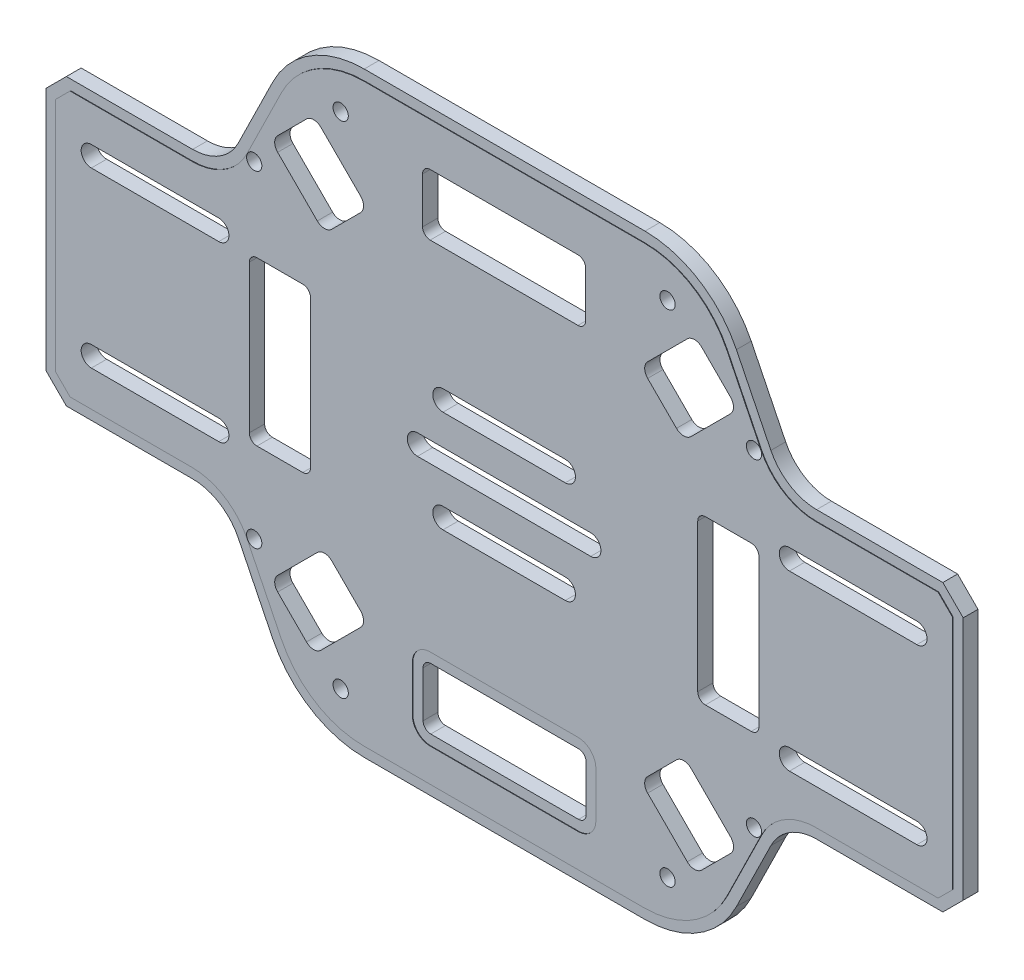
SolidWorks part; units mm, degrees
ref_plane "Alzado" through (0, 0, 0) normal (0, 0, 1) x (1, 0, 0)
ref_plane "Planta" through (0, 0, 0) normal (0, 1, 0) x (1, 0, 0)
ref_plane "Vista lateral" through (0, 0, 0) normal (1, 0, 0) x (0, 0, -1)
sketch "Croquis1" plane through (0, 0, 0) normal (0, 0, 1) x (1, 0, 0)
  line L0 (0, -28) -> (0, 28)
  line L1 (90, 0) -> (90, 79.6309) construction
  line L2 (117.5482, 58.5) -> (62.4518, 58.5)
  line L3 (180, 28) -> (151.2259, 28)
  line L4 (142.2524, 33.5868) -> (135.4952, 47.3264)
  line L5 (0, -28) -> (28.7741, -28)
  line L6 (180, 28) -> (180, -28)
  line L7 (0, 0) -> (180, 0) construction
  line L8 (0, 28) -> (28.7741, 28)
  line L9 (37.7476, 33.5868) -> (44.5048, 47.3264)
  line L10 (37.7476, -33.5868) -> (44.5048, -47.3264)
  line L11 (117.5482, -58.5) -> (62.4518, -58.5)
  line L12 (142.2524, -33.5868) -> (135.4952, -47.3264)
  line L13 (180, -28) -> (151.2259, -28)
  line L14 (78, -8) -> (102, -8)
  line L15 (107, -2) -> (73, -2)
  line L16 (78, 12) -> (102, 12)
  line L17 (107, 2) -> (73, 2)
  line L18 (78, -12) -> (102, -12)
  line L19 (78, 8) -> (102, 8)
  line L20 (106, -46.5) -> (106, -37.5)
  line L21 (75.5, 48) -> (104.5, 48)
  line L22 (74, 46.5) -> (74, 37.5)
  line L23 (75.5, 36) -> (104.5, 36)
  line L24 (40, 14.5) -> (40, -14.5)
  line L25 (106, 46.5) -> (106, 37.5)
  line L26 (74, 48) -> (106, 36) construction
  line L27 (74, 36) -> (106, 48) construction
  line L28 (74, -46.5) -> (74, -37.5)
  line L29 (75.5, -48) -> (104.5, -48)
  line L30 (75.5, -36) -> (104.5, -36)
  line L31 (146, -19) -> (171, -19)
  line L32 (129.5, 16) -> (138.5, 16)
  line L33 (128, 14.5) -> (128, -14.5)
  line L34 (129.5, -16) -> (138.5, -16)
  line L35 (140, 14.5) -> (140, -14.5)
  line L36 (128, 16) -> (140, -16) construction
  line L37 (128, -16) -> (140, 16) construction
  line L38 (50.5, -16) -> (41.5, -16)
  line L39 (52, 14.5) -> (52, -14.5)
  line L40 (50.5, 16) -> (41.5, 16)
  line L41 (146, 19) -> (171, 19)
  line L42 (146, -15) -> (171, -15)
  line L43 (146, 15) -> (171, 15)
  line L44 (34, -15) -> (9, -15)
  line L45 (34, -19) -> (9, -19)
  line L46 (34, 19) -> (9, 19)
  line L47 (34, 15) -> (9, 15)
  arc A0 (44.5048, 47.3264) -> (62.4518, 58.5) centre (62.4518, 38.5) cw
  arc A1 (28.7741, 28) -> (37.7476, 33.5868) centre (28.7741, 38) ccw
  arc A2 (151.2259, 28) -> (142.2524, 33.5868) centre (151.2259, 38) cw
  arc A3 (135.4952, 47.3264) -> (117.5482, 58.5) centre (117.5482, 38.5) ccw
  arc A4 (28.7741, -28) -> (37.7476, -33.5868) centre (28.7741, -38) cw
  arc A5 (44.5048, -47.3264) -> (62.4518, -58.5) centre (62.4518, -38.5) ccw
  arc A6 (135.4952, -47.3264) -> (117.5482, -58.5) centre (117.5482, -38.5) cw
  arc A7 (151.2259, -28) -> (142.2524, -33.5868) centre (151.2259, -38) ccw
  arc A8 (73, 2) -> (73, -2) centre (73, 0) ccw
  arc A9 (107, -2) -> (107, 2) centre (107, 0) ccw
  arc A10 (78, 12) -> (78, 8) centre (78, 10) ccw
  arc A11 (102, 8) -> (102, 12) centre (102, 10) ccw
  arc A12 (78, -12) -> (78, -8) centre (78, -10) cw
  arc A13 (102, -8) -> (102, -12) centre (102, -10) cw
  arc A14 (104.5, 36) -> (106, 37.5) centre (104.5, 37.5) ccw
  arc A15 (104.5, 48) -> (106, 46.5) centre (104.5, 46.5) cw
  arc A16 (75.5, 48) -> (74, 46.5) centre (75.5, 46.5) ccw
  arc A17 (74, 37.5) -> (75.5, 36) centre (75.5, 37.5) ccw
  arc A18 (104.5, -36) -> (106, -37.5) centre (104.5, -37.5) cw
  arc A19 (104.5, -48) -> (106, -46.5) centre (104.5, -46.5) ccw
  arc A20 (75.5, -48) -> (74, -46.5) centre (75.5, -46.5) cw
  arc A21 (74, -37.5) -> (75.5, -36) centre (75.5, -37.5) cw
  arc A22 (138.5, -16) -> (140, -14.5) centre (138.5, -14.5) ccw
  arc A23 (128, -14.5) -> (129.5, -16) centre (129.5, -14.5) ccw
  arc A24 (138.5, 16) -> (140, 14.5) centre (138.5, 14.5) cw
  arc A25 (129.5, 16) -> (128, 14.5) centre (129.5, 14.5) ccw
  arc A26 (50.5, 16) -> (52, 14.5) centre (50.5, 14.5) cw
  arc A27 (41.5, 16) -> (40, 14.5) centre (41.5, 14.5) ccw
  arc A28 (41.5, -16) -> (40, -14.5) centre (41.5, -14.5) cw
  arc A29 (52, -14.5) -> (50.5, -16) centre (50.5, -14.5) cw
  arc A30 (146, 19) -> (146, 15) centre (146, 17) ccw
  arc A31 (171, 15) -> (171, 19) centre (171, 17) ccw
  arc A32 (171, -15) -> (171, -19) centre (171, -17) cw
  arc A33 (146, -19) -> (146, -15) centre (146, -17) cw
  arc A34 (34, -19) -> (34, -15) centre (34, -17) ccw
  arc A35 (9, -15) -> (9, -19) centre (9, -17) ccw
  arc A36 (9, 15) -> (9, 19) centre (9, 17) cw
  arc A37 (34, 19) -> (34, 15) centre (34, 17) cw
  point P15 (50, 58.5)
  point P18 (35, 28)
  point P22 (90, 58.5)
  point P41 (90, 10)
  point P55 (90, 42)
  point P84 (134, 0)
  point P113 (158.5, 17)
  dimension "D7" = 20
  dimension "D8" = 10
  dimension "D16" = 1.5
  dimension "D20" = 1.5
  dimension "D1" = 180
  dimension "D2" = 28
  dimension "D3" = 40
  dimension "D4" = 4
  dimension "D5" = 35
  dimension "D6" = 58.5
  dimension "D9" = 34
  dimension "D10" = 24
  dimension "D11" = 4
  dimension "D12" = 10
  dimension "D13" = 12
  dimension "D14" = 32
  dimension "D15" = 42
  dimension "D17" = 32
  dimension "D18" = 12
  dimension "D19" = 44
  dimension "D21" = 25
  dimension "D22" = 4
  dimension "D23" = 17
  dimension "D24" = 24.5
extrude "Saliente-Extruir1" add sketch "Croquis1" along normal mid plane 3
chamfer "Chaflán1" distance 4 angle 45 4 edges at (0, 28, 0) (0, -28, 0) (180, 28, 0) (180, -28, 0)
sketch "Croquis2" plane through (0, 0, 1.5) normal (0, 0, 1) x (1, 0, 0)
  line L0 (117.5482, 58.5) -> (62.4518, 58.5) construction
  line L1 (142.2524, 33.5868) -> (135.4952, 47.3264) construction
  line L2 (176, 28) -> (151.2259, 28) construction
  line L3 (180, 24) -> (176, 28) construction
  line L4 (180, -24) -> (180, 24) construction
  line L5 (176, -28) -> (180, -24) construction
  line L6 (151.2259, -28) -> (176, -28) construction
  line L7 (135.4952, -47.3264) -> (142.2524, -33.5868) construction
  line L8 (62.4518, -58.5) -> (117.5482, -58.5) construction
  line L9 (37.7476, -33.5868) -> (44.5048, -47.3264) construction
  line L10 (4, -28) -> (28.7741, -28) construction
  line L11 (0, -24) -> (4, -28) construction
  line L12 (0, 24) -> (0, -24) construction
  line L13 (4, 28) -> (0, 24) construction
  line L14 (28.7741, 28) -> (4, 28) construction
  line L15 (44.5048, 47.3264) -> (37.7476, 33.5868) construction
  line L16 (117.5482, 58.5) -> (62.4518, 58.5)
  line L17 (142.2524, 33.5868) -> (135.4952, 47.3264)
  line L18 (176, 28) -> (151.2259, 28)
  line L19 (180, 24) -> (176, 28)
  line L20 (180, -24) -> (180, 24)
  line L21 (176, -28) -> (180, -24)
  line L22 (151.2259, -28) -> (176, -28)
  line L23 (135.4952, -47.3264) -> (142.2524, -33.5868)
  line L24 (62.4518, -58.5) -> (117.5482, -58.5)
  line L25 (37.7476, -33.5868) -> (44.5048, -47.3264)
  line L26 (4, -28) -> (28.7741, -28)
  line L27 (0, -24) -> (4, -28)
  line L28 (0, 24) -> (0, -24)
  line L29 (4, 28) -> (0, 24)
  line L30 (28.7741, 28) -> (4, 28)
  line L31 (44.5048, 47.3264) -> (37.7476, 33.5868)
  line L32 (140.4577, 32.7042) -> (133.7005, 46.4438)
  line L33 (117.5482, 56.5) -> (62.4518, 56.5)
  line L34 (46.2995, 46.4438) -> (39.5423, 32.7042)
  line L35 (28.7741, 26) -> (4.8284, 26)
  line L36 (4.8284, 26) -> (2, 23.1716)
  line L37 (2, 23.1716) -> (2, -23.1716)
  line L38 (2, -23.1716) -> (4.8284, -26)
  line L39 (4.8284, -26) -> (28.7741, -26)
  line L40 (39.5423, -32.7042) -> (46.2995, -46.4438)
  line L41 (62.4518, -56.5) -> (117.5482, -56.5)
  line L42 (133.7005, -46.4438) -> (140.4577, -32.7042)
  line L43 (151.2259, -26) -> (175.1716, -26)
  line L44 (175.1716, -26) -> (178, -23.1716)
  line L45 (178, -23.1716) -> (178, 23.1716)
  line L46 (178, 23.1716) -> (175.1716, 26)
  line L47 (175.1716, 26) -> (151.2259, 26)
  arc A0 (62.4518, 58.5) -> (44.5048, 47.3264) centre (62.4518, 38.5) ccw construction
  arc A1 (135.4952, 47.3264) -> (117.5482, 58.5) centre (117.5482, 38.5) ccw construction
  arc A2 (142.2524, 33.5868) -> (151.2259, 28) centre (151.2259, 38) ccw construction
  arc A3 (151.2259, -28) -> (142.2524, -33.5868) centre (151.2259, -38) ccw construction
  arc A4 (117.5482, -58.5) -> (135.4952, -47.3264) centre (117.5482, -38.5) ccw construction
  arc A5 (44.5048, -47.3264) -> (62.4518, -58.5) centre (62.4518, -38.5) ccw construction
  arc A6 (37.7476, -33.5868) -> (28.7741, -28) centre (28.7741, -38) ccw construction
  arc A7 (28.7741, 28) -> (37.7476, 33.5868) centre (28.7741, 38) ccw construction
  arc A8 (62.4518, 58.5) -> (44.5048, 47.3264) centre (62.4518, 38.5) ccw
  arc A9 (135.4952, 47.3264) -> (117.5482, 58.5) centre (117.5482, 38.5) ccw
  arc A10 (142.2524, 33.5868) -> (151.2259, 28) centre (151.2259, 38) ccw
  arc A11 (151.2259, -28) -> (142.2524, -33.5868) centre (151.2259, -38) ccw
  arc A12 (117.5482, -58.5) -> (135.4952, -47.3264) centre (117.5482, -38.5) ccw
  arc A13 (44.5048, -47.3264) -> (62.4518, -58.5) centre (62.4518, -38.5) ccw
  arc A14 (37.7476, -33.5868) -> (28.7741, -28) centre (28.7741, -38) ccw
  arc A15 (28.7741, 28) -> (37.7476, 33.5868) centre (28.7741, 38) ccw
  arc A16 (133.7005, 46.4438) -> (117.5482, 56.5) centre (117.5482, 38.5) ccw
  arc A17 (62.4518, 56.5) -> (46.2995, 46.4438) centre (62.4518, 38.5) ccw
  arc A18 (28.7741, 26) -> (39.5423, 32.7042) centre (28.7741, 38) ccw
  arc A19 (39.5423, -32.7042) -> (28.7741, -26) centre (28.7741, -38) ccw
  arc A20 (46.2995, -46.4438) -> (62.4518, -56.5) centre (62.4518, -38.5) ccw
  arc A21 (117.5482, -56.5) -> (133.7005, -46.4438) centre (117.5482, -38.5) ccw
  arc A22 (151.2259, -26) -> (140.4577, -32.7042) centre (151.2259, -38) ccw
  arc A23 (140.4577, 32.7042) -> (151.2259, 26) centre (151.2259, 38) ccw
  dimension "D1" = 2
extrude "Cortar-Extruir1" cut sketch "Croquis2" against normal blind 0.1
sketch "Croquis3" plane through (0, 0, 1.5) normal (0, 0, 1) x (1, 0, 0)
  line L0 (74, -37.5) -> (74, -46.5) construction
  line L1 (75.5, -48) -> (104.5, -48) construction
  line L2 (106, -46.5) -> (106, -37.5) construction
  line L3 (104.5, -36) -> (75.5, -36) construction
  line L4 (74, -37.5) -> (74, -46.5)
  line L5 (75.5, -48) -> (104.5, -48)
  line L6 (106, -46.5) -> (106, -37.5)
  line L7 (104.5, -36) -> (75.5, -36)
  line L8 (72, -37.5) -> (72, -46.5)
  line L9 (75.5, -50) -> (104.5, -50)
  line L10 (108, -46.5) -> (108, -37.5)
  line L11 (104.5, -34) -> (75.5, -34)
  arc A0 (104.5, -48) -> (106, -46.5) centre (104.5, -46.5) ccw construction
  arc A1 (106, -37.5) -> (104.5, -36) centre (104.5, -37.5) ccw construction
  arc A2 (75.5, -36) -> (74, -37.5) centre (75.5, -37.5) ccw construction
  arc A3 (74, -46.5) -> (75.5, -48) centre (75.5, -46.5) ccw construction
  arc A4 (104.5, -48) -> (106, -46.5) centre (104.5, -46.5) ccw
  arc A5 (106, -37.5) -> (104.5, -36) centre (104.5, -37.5) ccw
  arc A6 (75.5, -36) -> (74, -37.5) centre (75.5, -37.5) ccw
  arc A7 (74, -46.5) -> (75.5, -48) centre (75.5, -46.5) ccw
  arc A8 (72, -46.5) -> (75.5, -50) centre (75.5, -46.5) ccw
  arc A9 (104.5, -50) -> (108, -46.5) centre (104.5, -46.5) ccw
  arc A10 (108, -37.5) -> (104.5, -34) centre (104.5, -37.5) ccw
  arc A11 (75.5, -34) -> (72, -37.5) centre (75.5, -37.5) ccw
  dimension "D1" = 2
extrude "Cortar-Extruir2" cut sketch "Croquis3" against normal blind 0.1
sketch "Croquis4" plane through (0, 0, 1.5) normal (0, 0, 1) x (1, 0, 0)
  line L0 (26.3604, 63.6396) -> (50.402, 39.598) construction
  line L1 (132.6734, 32.1734) -> (111.6734, 32.1734) construction
  line L2 (131.3657, 41.3657) -> (90, 0) construction
  line L3 (122.2738, 15.3032) -> (139.0435, 32.0729) construction
  line L4 (110.3154, 20.1734) -> (110.3154, 44.1734) construction
  line L5 (133.8406, 43.8406) -> (90, 0) construction
  line L7 (90, -23.3345) -> (90.3345, -23) construction
  line L8 (145.5079, 32.1734) -> (122.1734, 55.5079)
  line L9 (66.6655, 0) -> (67, 0.3345) construction
  line L10 (46.1594, 43.8406) -> (50.402, 39.598) construction
  line L11 (126.0624, 36.0624) -> (118.2843, 28.2843) construction
  line L13 (133.8406, -43.8406) -> (145.5079, -32.1734)
  line L14 (145.5079, -32.1734) -> (101.6673, 11.6673) construction
  line L15 (34.4921, 32.1734) -> (46.1594, 43.8406)
  line L16 (129.598, 32.5269) -> (125.6878, 28.6168)
  line L17 (118.6589, 35.7299) -> (114.7487, 31.8198)
  line L18 (126.0624, -36.0624) -> (118.2843, -28.2843) construction
  line L19 (122.5269, -39.598) -> (114.7487, -31.8198)
  line L24 (53.9376, 36.0624) -> (61.7157, 28.2843) construction
  line L31 (67, 0.3345) -> (67, -0.3345) construction
  line L34 (78.25, -39) -> (101.75, -39) construction
  line L35 (78.25, -36.5) -> (101.75, -36.5)
  line L36 (78.25, -41.5) -> (101.75, -41.5)
  line L37 (89.6655, -23) -> (90.3345, -23) construction
  line L43 (99.5, 23) -> (80.5, 23) construction
  line L44 (99.5, 18.25) -> (80.5, 18.25)
  line L45 (99.5, 27.75) -> (80.5, 27.75)
  line L46 (129, -11.75) -> (129, 11.75) construction
  line L47 (126.5, -11.75) -> (126.5, 11.75)
  line L48 (131.5, -11.75) -> (131.5, 11.75)
  line L49 (113, -0.3345) -> (113, 9.5) construction
  line L50 (108.25, -9.5) -> (108.25, 9.5)
  line L51 (117.75, -9.5) -> (117.75, 9.5)
  line L52 (95.0845, 18.25) -> (85.5845, 27.75) construction
  line L53 (84.9155, 18.25) -> (122.1734, 55.5079) construction
  line L54 (71.75, -5.0845) -> (66.6655, 0) construction
  line L55 (101.6673, -11.6673) -> (145.5079, 32.1734) construction
  line L56 (90, -23) -> (90, -23.3345) construction
  line L57 (90, -41.5) -> (90, -48.5)
  line L58 (105.3032, 32.2738) -> (122.0729, 49.0435) construction
  line L59 (139.0435, 32.0729) -> (122.0729, 49.0435) construction
  line L60 (110.3154, 20.1734) -> (134.0313, 44.1734) construction
  line L61 (110.3154, 44.1734) -> (134.0313, 20.1734) construction
  line L62 (132.8655, 41.6734) -> (111.4812, 41.6734) construction
  line L63 (132.8655, 41.6734) -> (132.8655, 22.6734) construction
  line L64 (132.8655, 22.6734) -> (111.4812, 22.6734) construction
  line L65 (111.4812, 41.6734) -> (111.4812, 22.6734) construction
  line L66 (132.8655, 41.6734) -> (111.4812, 22.6734) construction
  line L67 (132.8655, 22.6734) -> (111.4812, 41.6734) construction
  line L68 (53.9376, 36.0624) -> (133.8406, -43.8406) construction
  line L69 (53.9376, 36.0624) -> (153.6396, -63.6396) construction
  line L71 (50.402, -39.598) -> (48.6343, -41.3657) construction
  line L72 (50.402, -39.598) -> (46.1594, -43.8406) construction
  line L73 (94.4155, -27.75) -> (99.5, -27.75)
  line L74 (90, -23.3345) -> (89.6655, -23) construction
  line L75 (90, -36.5) -> (90, -48.6956) construction
  arc A0 (99.8995, -9.8995) -> (80.1005, 9.8995) centre (90, 0) ccw
  arc A1 (129.598, 32.5269) -> (122.5269, 39.598) centre (126.0624, 36.0624) ccw
  arc A2 (114.7487, 31.8198) -> (121.8198, 24.7487) centre (118.2843, 28.2843) ccw
  arc A3 (122.5269, -39.598) -> (129.598, -32.5269) centre (126.0624, -36.0624) ccw
  arc A4 (121.8198, -24.7487) -> (114.7487, -31.8198) centre (118.2843, -28.2843) ccw
  arc A7 (50.402, 39.598) -> (50.402, 32.5269) centre (53.9376, 36.0624) ccw
  arc A8 (58.1802, 24.7487) -> (65.2513, 31.8198) centre (61.7157, 28.2843) ccw
  arc A13 (78.25, -36.5) -> (78.25, -41.5) centre (78.25, -39) ccw
  arc A16 (99.5, -27.75) -> (99.5, -18.25) centre (99.5, -23) ccw
  arc A17 (101.75, 36.5) -> (101.75, 41.5) centre (101.75, 39) ccw
  arc A18 (78.25, 41.5) -> (78.25, 36.5) centre (78.25, 39) ccw
  arc A21 (126.5, -11.75) -> (131.5, -11.75) centre (129, -11.75) ccw
  arc A22 (131.5, 11.75) -> (126.5, 11.75) centre (129, 11.75) ccw
  arc A28 (145.5079, 32.1734) -> (145.5079, -32.1734) centre (218.0762, 0) ccw
  circle A29 centre (122.0729, 49.0435) radius 1.5
  circle A30 centre (139.0435, 32.0729) radius 1.5
  circle A31 centre (111.4812, 41.6734) radius 1.5
  circle A32 centre (111.4812, 22.6734) radius 1.5
  point P8 (122.1734, 32.1734)
  point P11 (90, 0)
  point P13 (90, 0)
  point P18 (90, 0)
  point P30 (122.1734, 32.1734)
  point P42 (122.1734, -32.1734)
  point P49 (57.8266, -32.1734)
  point P56 (57.8266, 32.1734)
  point P61 (90, 0)
  point P65 (51, 0)
  point P72 (67, 0)
  point P76 (90, -39)
  point P83 (90, -23)
  point P93 (90, 39)
  point P100 (90, 23)
  point P107 (129, 0)
  point P114 (113, 0)
  point P119 (90, 0)
  point P136 (90, 0)
  point P139 (122.1734, 32.1734)
  dimension "D15" = 3
  dimension "D5" = 24
  dimension "D6" = 10
  dimension "D7" = 45.5
  dimension "D10" = 5
  dimension "D11" = 23
  dimension "D12" = 39
  dimension "D13" = 7
  dimension "D14" = 19
extrude "Cortar-Extruir3" cut sketch "Croquis4" against normal blind 24.1 contours A29 | A30
sketch "Croquis5" plane through (0, 0, 1.5) normal (0, 0, 1) x (1, 0, 0)
  circle A0 centre (90, 0) radius 25.8275 construction
  circle A1 centre (139.0435, 32.0729) radius 1.5 construction
  circle A2 centre (122.0729, 49.0435) radius 1.5 construction
  circle A3 centre (139.0435, 32.0729) radius 1.5 construction
  circle A4 centre (122.0729, 49.0435) radius 1.5 construction
  circle A5 centre (139.0435, -32.0729) radius 1.5
  circle A6 centre (122.0729, -49.0435) radius 1.5
  circle A7 centre (90, 0) radius 25.8275 construction
  circle A8 centre (57.9271, -49.0435) radius 1.5
  circle A9 centre (40.9565, -32.0729) radius 1.5
  circle A10 centre (90, 0) radius 25.8275 construction
  circle A11 centre (40.9565, 32.0729) radius 1.5
  circle A12 centre (57.9271, 49.0435) radius 1.5
  circle A13 centre (90, 0) radius 25.8275 construction
  point P26 (90, 0)
  dimension "D1" = 4
extrude "Cortar-Extruir4" cut sketch "Croquis5" against normal blind 24.1
sketch "Croquis6" plane through (0, 0, 1.5) normal (0, 0, 1) x (1, 0, 0)
  line L0 (139.0435, 32.0729) -> (122.0729, 49.0435) construction
  line L1 (130.5582, 40.5582) -> (116.8318, 26.8318) construction
  line L2 (126.6574, -28.1721) -> (134.4355, -35.9502)
  line L3 (118.1721, 33.8289) -> (123.8289, 28.1721)
  line L4 (118.1721, 36.6574) -> (125.9502, 44.4355)
  line L5 (128.7787, 44.4355) -> (134.4355, 38.7787)
  line L6 (126.6574, 28.1721) -> (134.4355, 35.9502)
  line L7 (116.7579, 35.2431) -> (135.8497, 37.3645) construction
  line L8 (127.3645, 45.8497) -> (125.2431, 26.7579) construction
  line L9 (118.1721, -36.6574) -> (125.9502, -44.4355)
  line L10 (123.8289, -28.1721) -> (118.1721, -33.8289)
  line L11 (134.4355, -38.7787) -> (128.7787, -44.4355)
  line L12 (61.8279, -36.6574) -> (54.0498, -44.4355)
  line L13 (53.3426, -28.1721) -> (45.5645, -35.9502)
  line L14 (61.8279, -33.8289) -> (56.1711, -28.1721)
  line L15 (51.2213, -44.4355) -> (45.5645, -38.7787)
  line L16 (53.3426, 28.1721) -> (45.5645, 35.9502)
  line L17 (61.8279, 36.6574) -> (54.0498, 44.4355)
  line L18 (56.1711, 28.1721) -> (61.8279, 33.8289)
  line L19 (45.5645, 38.7787) -> (51.2213, 44.4355)
  arc A0 (134.4355, 38.7787) -> (134.4355, 35.9502) centre (133.0213, 37.3645) cw
  arc A1 (123.8289, 28.1721) -> (126.6574, 28.1721) centre (125.2431, 29.5863) ccw
  arc A2 (118.1721, 33.8289) -> (118.1721, 36.6574) centre (119.5863, 35.2431) cw
  arc A3 (125.9502, 44.4355) -> (128.7787, 44.4355) centre (127.3645, 43.0213) cw
  arc A4 (118.1721, -33.8289) -> (118.1721, -36.6574) centre (119.5863, -35.2431) ccw
  arc A5 (123.8289, -28.1721) -> (126.6574, -28.1721) centre (125.2431, -29.5863) cw
  arc A6 (134.4355, -35.9502) -> (134.4355, -38.7787) centre (133.0213, -37.3645) cw
  arc A7 (128.7787, -44.4355) -> (125.9502, -44.4355) centre (127.3645, -43.0213) cw
  arc A8 (56.1711, -28.1721) -> (53.3426, -28.1721) centre (54.7569, -29.5863) ccw
  arc A9 (61.8279, -33.8289) -> (61.8279, -36.6574) centre (60.4137, -35.2431) cw
  arc A10 (54.0498, -44.4355) -> (51.2213, -44.4355) centre (52.6355, -43.0213) cw
  arc A11 (45.5645, -38.7787) -> (45.5645, -35.9502) centre (46.9787, -37.3645) cw
  arc A12 (61.8279, 33.8289) -> (61.8279, 36.6574) centre (60.4137, 35.2431) ccw
  arc A13 (56.1711, 28.1721) -> (53.3426, 28.1721) centre (54.7569, 29.5863) cw
  arc A14 (45.5645, 35.9502) -> (45.5645, 38.7787) centre (46.9787, 37.3645) cw
  arc A15 (51.2213, 44.4355) -> (54.0498, 44.4355) centre (52.6355, 43.0213) cw
  point P61 (90, 0)
  dimension "D3" = 2
  dimension "D1" = 15
  dimension "D2" = 12
  dimension "D4" = 4
extrude "Cortar-Extruir5" cut sketch "Croquis6" against normal blind 24.1
